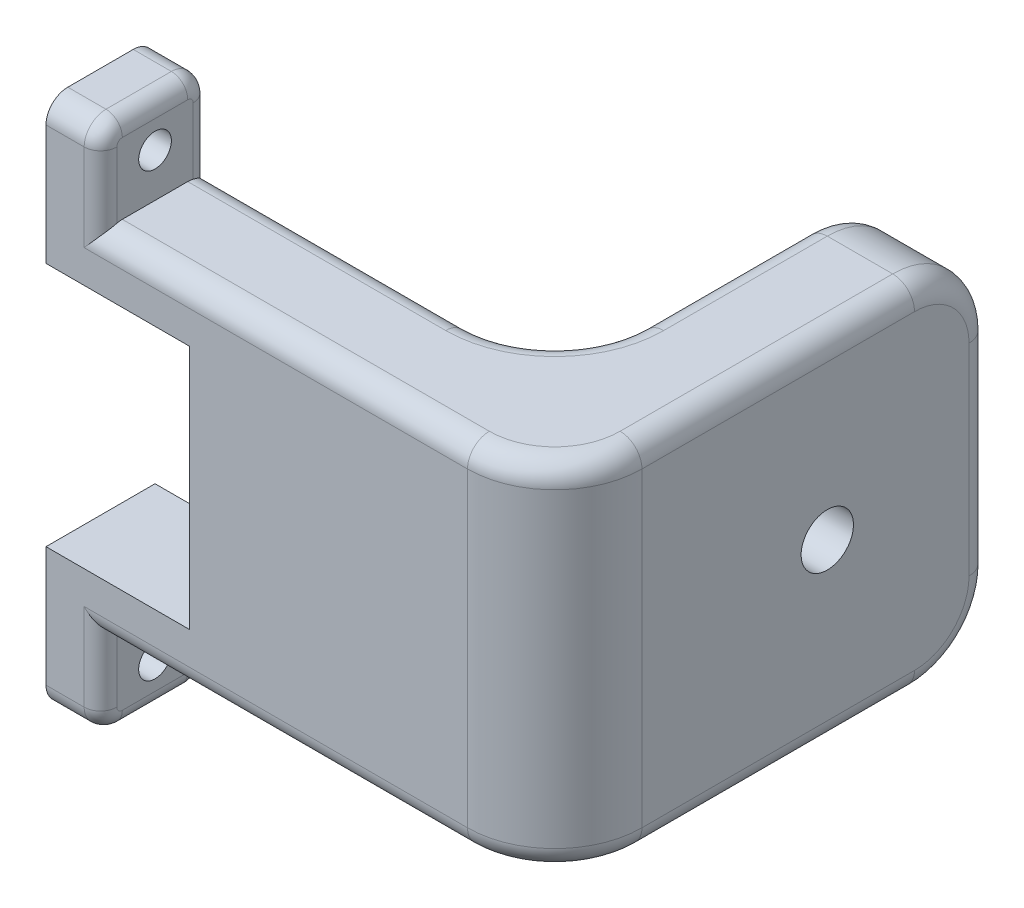
SolidWorks part; units mm, degrees
ref_plane "Front Plane" through (0, 0, 0) normal (0, 0, 1) x (1, 0, 0)
ref_plane "Top Plane" through (0, 0, 0) normal (0, 1, 0) x (1, 0, 0)
ref_plane "Right Plane" through (0, 0, 0) normal (1, 0, 0) x (0, 0, -1)
sketch "Sketch1" plane through (0, 0, 0) normal (0, 0, 1) x (1, 0, 0)
  line L0 (-7.0036, -14.9158) -> (6.175, -14.9158)
  line L1 (6.175, -14.9158) -> (6.175, 7.5842)
  line L2 (6.175, 7.5842) -> (-7.0036, 7.5842)
  line L6 (-7.0036, 7.5842) -> (-7.0036, 12.5842)
  line L7 (-7.0036, 12.5842) -> (9.6598, 12.5842)
  line L8 (9.6598, 12.5842) -> (9.6598, -19.9158)
  line L9 (9.6598, -19.9158) -> (-7.0036, -19.9158)
  line L10 (-7.0036, -19.9158) -> (-7.0036, -14.9158)
extrude "Boss-Extrude1" add sketch "Sketch1" along normal blind 15
sketch "Sketch2" plane through (9.6598, 0, 0) normal (1, 0, 0) x (0, 0, -1)
  line L4 (0, -19.9158) -> (0, 12.5842)
  line L5 (0, 12.5842) -> (-15, 12.5842)
  line L6 (-15, 12.5842) -> (-15, -19.9158)
  line L7 (-15, -19.9158) -> (0, -19.9158)
  line L8 (0, -19.9158) -> (0, 12.5842)
  line L9 (0, 12.5842) -> (-15, 12.5842)
  line L10 (-15, 12.5842) -> (-15, -19.9158)
  line L11 (-15, -19.9158) -> (0, -19.9158)
  dimension "D1" = 0
extrude "Boss-Extrude2" add sketch "Sketch2" along normal blind 30
sketch "Sketch3" plane through (0, 0, 0) normal (0, 0, -1) x (-1, 0, 0)
  line L0 (-39.6598, -19.9158) -> (7.0036, -19.9158) construction
  line L1 (-39.6598, 12.5842) -> (-29.6598, 12.5842)
  line L2 (-39.6598, 12.5842) -> (-39.6598, -19.9158)
  line L3 (-39.6598, -19.9158) -> (-29.6598, -19.9158)
  line L4 (-29.6598, 12.5842) -> (-29.6598, -19.9158)
  dimension "D1" = 10
extrude "Boss-Extrude3" add sketch "Sketch3" along normal blind 30
sketch "Sketch4" plane through (39.6598, 0, 0) normal (1, 0, 0) x (0, 0, -1)
  line L0 (30, -3.6658) -> (-15, -3.6658) construction
  line L1 (30, 12.5842) -> (30, -19.9158) construction
  line L2 (-15, 12.5842) -> (-15, -19.9158) construction
  circle A0 centre (15, -3.5398) radius 2.4
extrude "Cut-Extrude1" cut sketch "Sketch4" against normal blind 5
sketch "Sketch5" plane through (0, 0, 15) normal (0, 0, 1) x (1, 0, 0)
  line L8 (39.6598, 12.5842) -> (-7.0036, 12.5842)
  line L9 (-7.0036, 12.5842) -> (-7.0036, 7.5842)
  line L10 (-7.0036, 7.5842) -> (6.175, 7.5842)
  line L11 (6.175, 7.5842) -> (6.175, -14.9158)
  line L12 (6.175, -14.9158) -> (-7.0036, -14.9158)
  line L13 (-7.0036, -14.9158) -> (-7.0036, -19.9158)
  line L14 (-7.0036, -19.9158) -> (39.6598, -19.9158)
  line L15 (39.6598, -19.9158) -> (39.6598, 12.5842)
  line L16 (39.6598, 12.5842) -> (-7.0036, 12.5842)
  line L17 (-7.0036, 12.5842) -> (-7.0036, 7.5842)
  line L18 (-7.0036, 7.5842) -> (6.175, 7.5842)
  line L19 (6.175, 7.5842) -> (6.175, -14.9158)
  line L20 (6.175, -14.9158) -> (-7.0036, -14.9158)
  line L21 (-7.0036, -14.9158) -> (-7.0036, -19.9158)
  line L22 (-7.0036, -19.9158) -> (39.6598, -19.9158)
  line L23 (39.6598, -19.9158) -> (39.6598, 12.5842)
  dimension "D1" = 0
extrude "Cut-Extrude2" cut sketch "Sketch5" against normal blind 5
fillet "Fillet1" radius 7 2 edges at (34.6598, 12.5842, -30) (34.6598, -19.9158, -30)
fillet "Fillet2" radius 8 2 edges at (39.6598, -3.6658, 10) (29.6598, -3.6658, 0)
sketch "Sketch6" plane through (-7.0036, 0, 0) normal (-1, 0, 0) x (0, 0, 1)
  line L1 (0, 7.5842) -> (10, 7.5842)
  line L2 (0, 7.5842) -> (0, 18.5842)
  line L3 (2, 20.5842) -> (8, 20.5842)
  line L4 (10, 7.5842) -> (10, 18.5842)
  line L6 (17.3, -3.6658) -> (0, -3.6658) construction
  line L7 (17.3, -14.9158) -> (17.3, 7.5842) construction
  line L8 (0, 7.5842) -> (0, -14.9158) construction
  line L9 (10, -14.9158) -> (10, -25.9158)
  line L10 (2, -27.9158) -> (8, -27.9158)
  line L11 (0, -14.9158) -> (0, -25.9158)
  line L12 (0, -14.9158) -> (10, -14.9158)
  arc A0 (2, -27.9158) -> (0, -25.9158) centre (2, -25.9158) cw
  arc A1 (10, -25.9158) -> (8, -27.9158) centre (8, -25.9158) cw
  arc A2 (8, 20.5842) -> (10, 18.5842) centre (8, 18.5842) cw
  arc A3 (0, 18.5842) -> (2, 20.5842) centre (2, 18.5842) cw
  point P17 (0, -27.9158)
  point P20 (10, -27.9158)
  point P23 (10, 20.5842)
  point P26 (0, 20.5842)
  dimension "D1" = 2
extrude "Boss-Extrude4" add sketch "Sketch6" against normal blind 5
sketch "Sketch7" plane through (-2.0036, 0, 0) normal (1, 0, 0) x (0, 0, -1)
  line L0 (-5, -27.9158) -> (-5, -19.9158) construction
  line L1 (-2, -27.9158) -> (-8, -27.9158) construction
  line L2 (-10, -19.9158) -> (-2, -19.9158) construction
  line L3 (-5, 20.5842) -> (-5, 12.5842) construction
  line L4 (-8, 20.5842) -> (-2, 20.5842) construction
  line L5 (-2, 12.5842) -> (-10, 12.5842) construction
  circle A0 centre (-5, -23.9158) radius 1.5
  circle A1 centre (-5, 16.5842) radius 1.5
extrude "Cut-Extrude3" cut sketch "Sketch7" against normal through all
fillet "Fillet3" radius 2 18 edges at (14.8281, -19.9158, 10) (37.3166, -19.9158, 7.6569) (14.8281, 12.5842, 10) (37.3166, 12.5842, 7.6569) (39.6598, 12.5842, -10.5) (39.6598, 10.5339, -27.9497) (39.6598, -3.6658, -30) (39.6598, -17.8656, -27.9497) (9.8281, 12.5842, 0) (27.3166, 12.5842, -2.3431) (29.6598, 12.5842, -15.5) (29.6598, 10.5339, -27.9497) (29.6598, -3.6658, -30) (29.6598, -17.8656, -27.9497) (9.8281, -19.9158, 0) (27.3166, -19.9158, -2.3431) (39.6598, -19.9158, -10.5) (29.6598, -19.9158, -15.5)
fillet "Fillet4" radius 1.5 10 edges at (-2.0036, 14.5842, 0) (-2.0036, 19.9984, 0.5858) (-2.0036, 20.5842, 5) (-2.0036, 19.9984, 9.4142) (-2.0036, -21.9158, 0) (-2.0036, -27.33, 0.5858) (-2.0036, -27.9158, 5) (-2.0036, -21.9158, 10) (-2.0036, 14.5842, 10) (-2.0036, -27.33, 9.4142)
